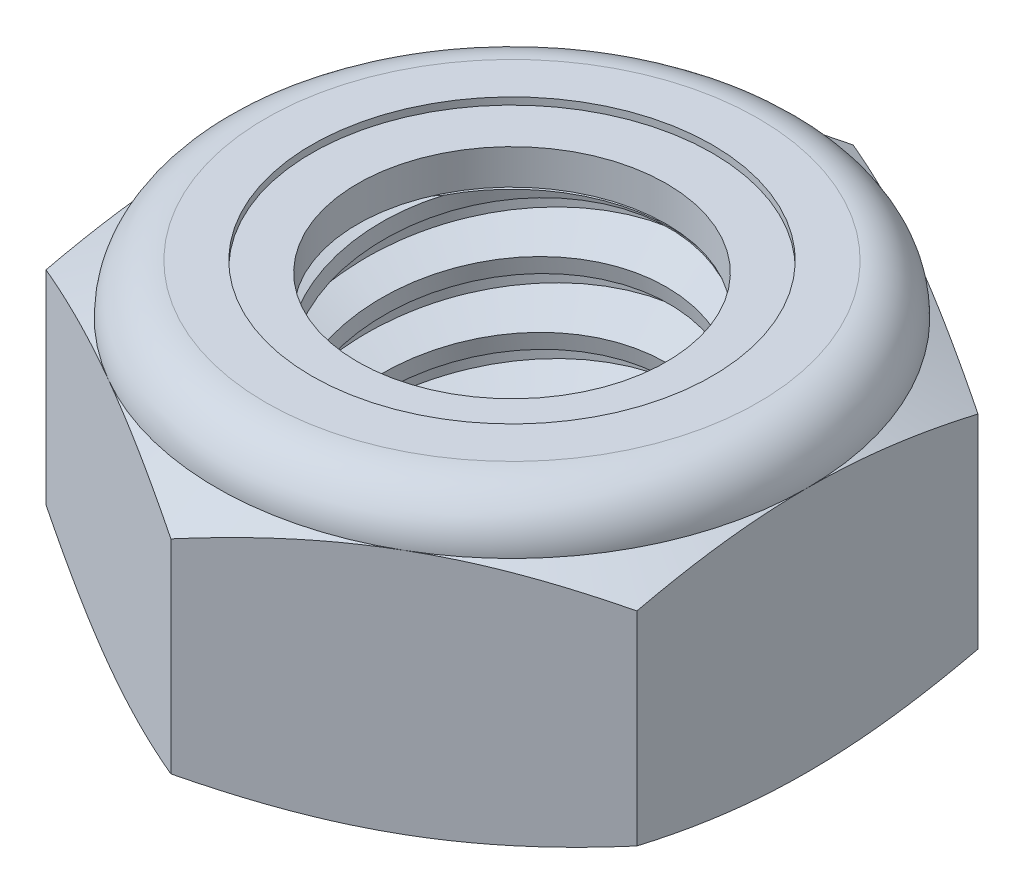
SolidWorks part; units mm, degrees
material "Alloy Steel"
ref_plane "Front" through (0, 0, 0) normal (0, 0, 1) x (1, 0, 0)
ref_plane "Top" through (0, 0, 0) normal (0, 1, 0) x (1, 0, 0)
ref_plane "Right" through (0, 0, 0) normal (1, 0, 0) x (0, 0, -1)
sketch "Sketch1" plane through (0, 0, 0) normal (0, 1, 0) x (1, 0, 0)
  line L1 (0, 7.3323) -> (-6.35, 3.6662)
  line L2 (-6.35, 3.6662) -> (-6.35, -3.6662)
  line L3 (-6.35, -3.6662) -> (0, -7.3323)
  line L4 (0, -7.3323) -> (6.35, -3.6662)
  line L5 (6.35, -3.6662) -> (6.35, 3.6662)
  line L6 (6.35, 3.6662) -> (0, 7.3323)
  circle A0 centre (0, 0) radius 6.35 construction
  dimension "Hex Flats" = 12.7
extrude "Extrude1" add sketch "Sketch1" along normal blind 6.35
sketch "Sketch2" plane through (0, 0, 0) normal (1, 0, 0) x (0, 0, -1)
  line L0 (-3.9624, 0) -> (-3.9624, 6.35) construction
  line L1 (0, 0) -> (3.9624, 0)
  line L2 (0, 0) -> (0, 6.35)
  line L3 (0, 6.35) -> (3.9624, 6.35)
  line L4 (3.9624, 0) -> (3.9624, 6.35)
  line L5 (-3.6662, 6.35) -> (3.6662, 6.35) construction
  line L7 (0, -3.9624) -> (0, 0) construction
  dimension "Thread Dia" = 7.9248
revolve "Revolve1" add sketch "Sketch2" angle 360 about L7
sketch "Sketch3" plane through (0, 0, 0) normal (1, 0, 0) x (0, 0, -1)
  line L0 (3.9624, 6.35) -> (-3.9624, 6.35) construction
  line L1 (-3.9624, 6.35) -> (-3.9624, 4.9389) construction
  line L2 (-3.9624, 4.9389) -> (3.9624, 6.35) construction
  line L3 (3.9624, 6.35) -> (3.9933, 6.1763) construction
  line L4 (3.9933, 6.1763) -> (4.2098, 4.9607)
  line L5 (4.2098, 4.9607) -> (3.3805, 5.261)
  line L6 (3.3805, 5.261) -> (3.3187, 5.6083)
  line L7 (3.3187, 5.6083) -> (3.9933, 6.1763)
  line L8 (3.3496, 5.4346) -> (4.1015, 5.5685) construction
  line L9 (3.9624, 6.35) -> (3.9624, 5.5438) construction
  line L10 (3.9624, 5.5438) -> (-3.9624, 4.1327) construction
  line L11 (-3.9624, 4.1327) -> (-3.9624, 4.9389) construction
  line L12 (-0.2692, 6.35) -> (0.2692, 3.3264) construction
  line L13 (-3.9624, 0) -> (-3.9624, 6.35) construction
  line L14 (0, 6.35) -> (3.9624, 6.35) construction
  line L15 (3.9624, 0) -> (3.9624, 6.35) construction
  point P13 (0, 4.8382)
  dimension "D1" = 0.1764
  dimension "D2" = 0.3528
  dimension "Thread Pitch" = 1.4111
  dimension "D4" = 60
  dimension "D5" = 1.4111
revolve "Cut-Revolve1" cut sketch "Sketch3" angle 360 about L12
pattern_linear "LPattern1" count 5 spacing 1.4111 along (0, -1, 0) count 2 spacing 1.4111 along (0, 1, 0) of "Cut-Revolve1"
sketch "Sketch4" plane through (0, 0, 0) normal (1, 0, 0) x (0, 0, -1)
  line L0 (0, 6.35) -> (3.9624, 6.35)
  line L1 (3.9624, 6.35) -> (3.3187, 6.0498)
  line L2 (3.3187, 6.0498) -> (3.3187, 0.3002)
  line L3 (3.3187, 0.3002) -> (3.9624, 0)
  line L4 (3.9624, 0) -> (0, 0)
  line L5 (0, 0) -> (0, 6.35)
  line L6 (3.9624, 0) -> (3.9624, 6.35) construction
  line L7 (0, 6.35) -> (3.9624, 6.35) construction
  line L8 (0, 0) -> (3.9624, 0) construction
  line L9 (0, 0) -> (0, 6.35) construction
  line L10 (0, 6.35) -> (0, 7.0603) construction
  dimension "D1" = 25
revolve "Cut-Revolve2" cut sketch "Sketch4" angle 360 about L10
combine bodies "Combine1" operation type subtract main body 112 bodies to subtract 111
sketch "Sketch5" plane through (0, 0, 0) normal (1, 0, 0) x (0, 0, -1)
  line L0 (0, 0) -> (6.35, 0)
  line L1 (6.35, 0) -> (7.3323, 0.4581)
  line L2 (7.3323, 0.4581) -> (7.3323, 4.8336)
  line L3 (7.3323, 4.8336) -> (6.35, 5.2917)
  line L4 (5.2917, 6.35) -> (5.2917, 7.62)
  line L5 (5.2917, 7.62) -> (8.6023, 7.62)
  line L6 (8.6023, 7.62) -> (8.6023, -1.27)
  line L7 (8.6023, -1.27) -> (0, -1.27)
  line L8 (0, -1.27) -> (0, 0)
  line L9 (6.35, 5.2917) -> (6.35, 0) construction
  line L10 (0, 0) -> (3.9624, 0) construction
  line L13 (7.3323, 2.6458) -> (8.6023, 2.6458) construction
  line L14 (7.3323, 6.35) -> (7.3323, 0) construction
  line L15 (0, 0) -> (0, 7.62) construction
  line L20 (0, 7.62) -> (5.2917, 7.62) construction
  line L22 (0, 6.35) -> (3.9624, 6.35) construction
  arc A0 (6.35, 5.2917) -> (5.2917, 6.35) centre (5.2917, 5.2917) ccw
  dimension "D1" = 25
  dimension "D2" = 1.27
  dimension "D3" = 6.35
  dimension "D4" = 1.0583
revolve "Cut-Revolve3" cut sketch "Sketch5" angle 360 about L15
sketch "Sketch6" plane through (0, 0, 0) normal (1, 0, 0) x (0, 0, -1)
  line L0 (0, 5.2917) -> (6.1976, 5.2917)
  line L1 (5.2917, 6.1976) -> (4.3052, 6.1976)
  line L2 (0, 7.62) -> (0, 5.2917)
  line L3 (4.3052, 7.62) -> (0, 7.62)
  line L4 (0, 7.62) -> (5.2917, 7.62) construction
  line L5 (0, 0) -> (0, 7.62) construction
  line L6 (0, 7.62) -> (0, 44.323) construction
  line L7 (4.3052, 6.1976) -> (4.3052, 7.62)
  line L8 (5.2917, 6.35) -> (5.2917, 6.1976) construction
  line L9 (4.3052, 6.1976) -> (3.3187, 6.1976) construction
  line L10 (3.3187, 6.1976) -> (3.3187, 6.0498) construction
  arc A0 (6.1976, 5.2917) -> (5.2917, 6.1976) centre (5.2917, 5.2917) ccw
  arc A1 (6.35, 5.2917) -> (5.2917, 6.35) centre (5.2917, 5.2917) ccw construction
  dimension "D1" = 0.1524
revolve "Cut-Revolve4" cut sketch "Sketch6" angle 360 about L6
sketch "Sketch7" plane through (0, 0, 0) normal (1, 0, 0) x (0, 0, -1)
  line L0 (3.3187, 5.3679) -> (6.1179, 5.3679)
  line L1 (5.2917, 6.1214) -> (3.3187, 6.1214)
  line L2 (3.3187, 6.1214) -> (3.3187, 5.3679)
  line L3 (3.3187, 5.3679) -> (0, 5.3679) construction
  line L4 (0, 5.3679) -> (0, 6.1214) construction
  line L5 (0, 6.1214) -> (3.3187, 6.1214) construction
  line L6 (3.3187, 5.3679) -> (3.3187, 5.2917) construction
  line L7 (0, 5.2917) -> (6.1976, 5.2917) construction
  line L8 (5.2917, 6.1214) -> (5.2917, 6.1976) construction
  arc A0 (6.1179, 5.3679) -> (5.2917, 6.1214) centre (5.2917, 5.2917) ccw
  arc A2 (6.1976, 5.2917) -> (5.2917, 6.1976) centre (5.2917, 5.2917) ccw construction
  dimension "D1" = 0.0762
revolve "Revolve2" add sketch "Sketch7" angle 360 about L4
equation "\"D1@Sketch3\"=\"Thread Pitch@Sketch3\"/8"
equation "\"D2@Sketch3\"=\"Thread Pitch@Sketch3\"/4"
equation "\"D5@Sketch3\"=\"Thread Pitch@Sketch3\""
equation "\"D4@LPattern1\"=\"Thread Pitch@Sketch3\""
equation "\"D3@LPattern1\"=\"Thread Pitch@Sketch3\""
equation "\"D1@LPattern1\"=\"Height@Extrude1\"/\"Thread Pitch@Sketch3\""
equation "\"D4@Sketch5\"=\"Height@Extrude1\"/6"
